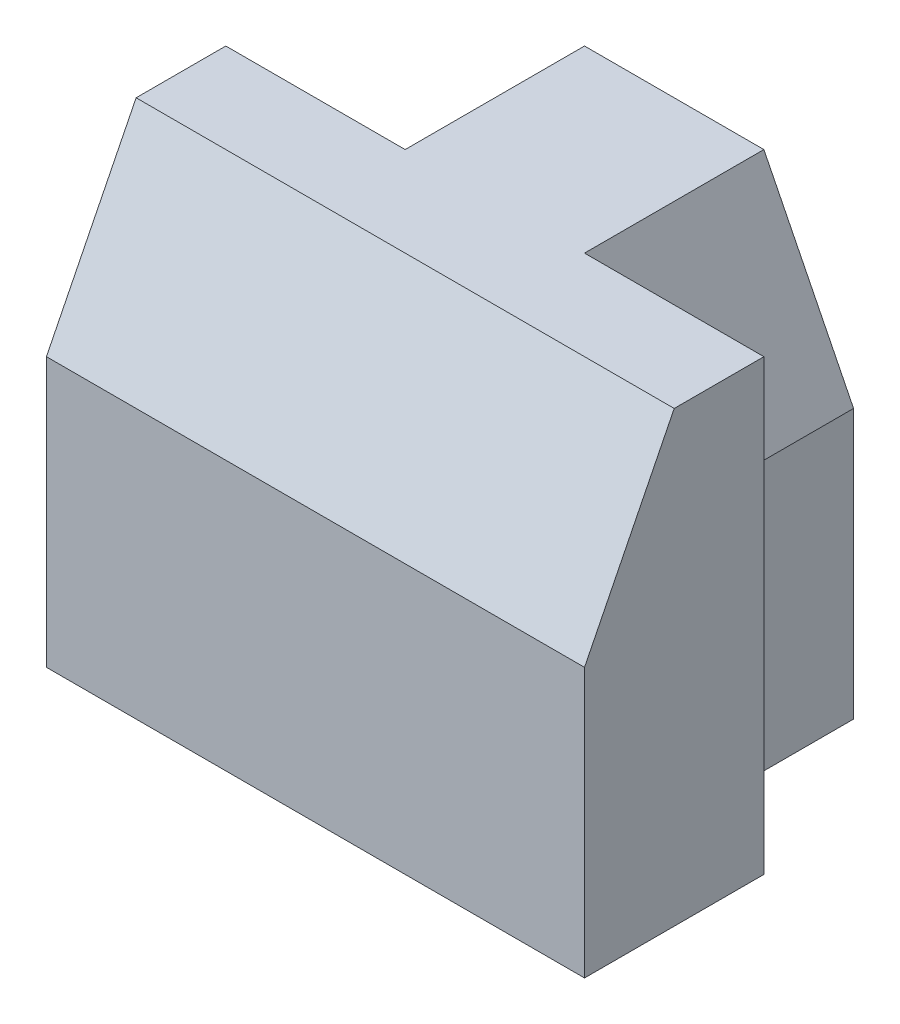
SolidWorks part; units mm, degrees
ref_plane "Front Plane" through (0, 0, 0) normal (0, 0, 1) x (1, 0, 0)
ref_plane "Top Plane" through (0, 0, 0) normal (0, 1, 0) x (1, 0, 0)
ref_plane "Right Plane" through (0, 0, 0) normal (1, 0, 0) x (0, 0, -1)
sketch "Sketch1" plane through (0, 0, 0) normal (0, 0, 1) x (1, 0, 0)
  line L1 (0, 0) -> (30, 0)
  line L2 (0, 0) -> (0, 25)
  line L3 (0, 25) -> (30, 25)
  line L4 (30, 0) -> (30, 25)
  dimension "D1" = 25
  dimension "D2" = 30
extrude "Boss-Extrude1" add sketch "Sketch1" along normal blind 20
sketch "Sketch2" plane through (0, 0, 0) normal (-1, 0, 0) x (0, 0, 1)
  line L0 (15, 25) -> (20, 15)
  line L1 (20, 25) -> (0, 25) construction
  line L2 (20, 25) -> (20, 0) construction
  line L3 (20, 15) -> (20, 25)
  line L4 (20, 25) -> (15, 25)
  dimension "D1" = 10
  dimension "D2" = 5
extrude "Cut-Extrude1" cut sketch "Sketch2" against normal blind 50
sketch "Sketch3" plane through (0, 0, 0) normal (0, 0, -1) x (-1, 0, 0)
  line L0 (-30, 25) -> (-20, 25)
  line L1 (-30, 25) -> (0, 25) construction
  line L2 (-20, 25) -> (-25, 15)
  line L3 (-25, 15) -> (-25, 0)
  line L4 (0, 0) -> (-30, 0) construction
  line L5 (-25, 0) -> (-30, 0)
  line L6 (-30, 0) -> (-30, 25)
  line L7 (0, 25) -> (-10, 25)
  line L8 (-10, 25) -> (-5, 15)
  line L9 (-5, 15) -> (-5, 0)
  line L10 (-5, 0) -> (0, 0)
  line L11 (0, 0) -> (0, 25)
  line L12 (0, 0) -> (0, 25)
  line M11 (0, 0) -> (0, 25)
  line M12 (0, 25) -> (-30, 25)
  line M13 (-30, 25) -> (-30, 0)
  line M14 (-30, 0) -> (0, 0)
  dimension "D1" = 10
  dimension "D2" = 10
  dimension "D3" = 5
  dimension "D4" = 5
  dimension "D5" = 10
  dimension "D6" = 10
  dimension "D7" = 20
extrude "Cut-Extrude2" cut sketch "Sketch3" against normal blind 10 contours L3 L2 M12 M13 M14 | L8 L9 M14 M11 M12
